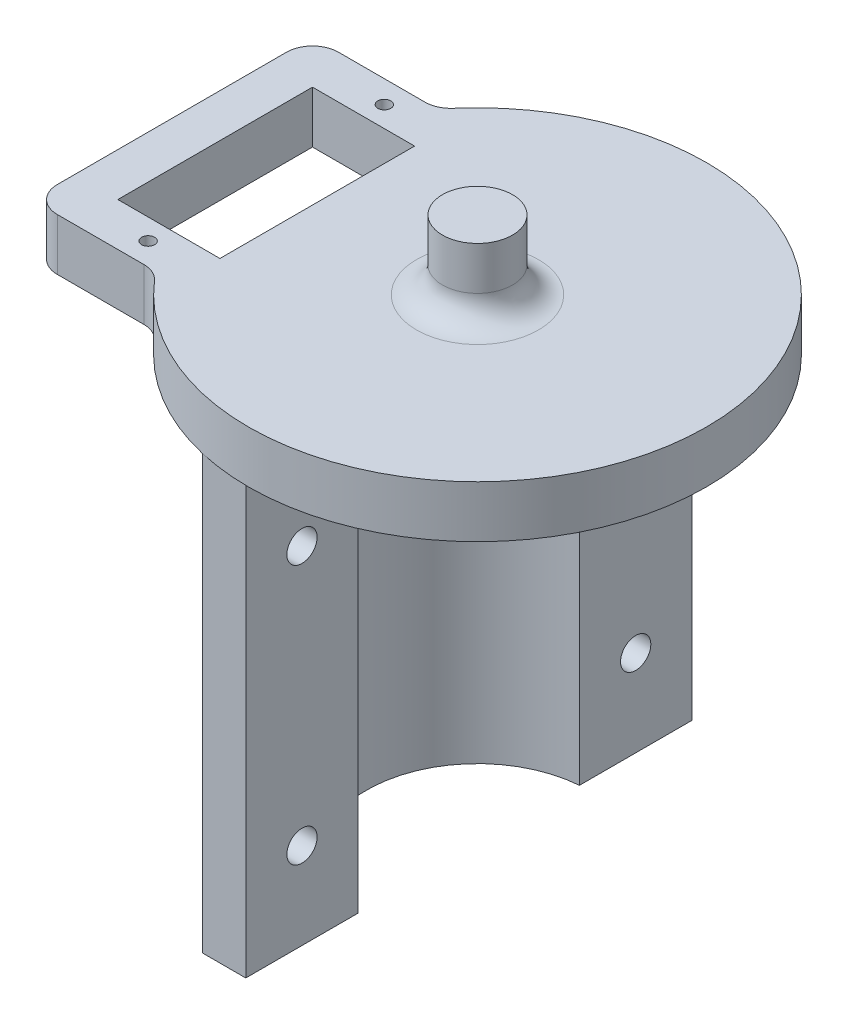
SolidWorks part; units mm, degrees
ref_plane "Front Plane" through (0, 0, 0) normal (0, 0, 1) x (1, 0, 0)
ref_plane "Top Plane" through (0, 0, 0) normal (0, 1, 0) x (1, 0, 0)
ref_plane "Right Plane" through (0, 0, 0) normal (1, 0, 0) x (0, 0, -1)
sketch "Sketch6" plane through (0, 0, 0) normal (0, -1, 0) x (1, 0, 0)
  line L5 (-1, 25.7848) -> (-1, 12.786)
  line L6 (-1, 25.7848) -> (-6, 25.7848)
  line L7 (-6, 25.7848) -> (-6, 16.7848)
  line L8 (-6, -16.7848) -> (-6, -25.7848)
  line L9 (-6, -25.7848) -> (-1, -25.7848)
  line L10 (-1, -25.7848) -> (-1, -12.786)
  line L11 (-12.825, 0) -> (-17.825, 0) construction
  arc A0 (-1, 12.786) -> (-1, -12.786) centre (0, 0) ccw
  arc A1 (-6, 16.7848) -> (-6, -16.7848) centre (0, 0) ccw
  dimension "D1" = 25.65
  dimension "D2" = 5
  dimension "D3" = 1
  dimension "D4" = 9
extrude "Boss-Extrude4" add sketch "Sketch6" along normal blind 50
sketch "Sketch7" plane through (-1, 0, 0) normal (1, 0, 0) x (0, 0, -1)
  line L0 (-19.2854, -50) -> (-19.2854, 0) construction
  line L3 (0, 0) -> (0, -50) construction
  line L6 (-25.7848, -25) -> (25.7848, -25) construction
  line L11 (-12.786, 0) -> (-25.7848, 0) construction
  line L12 (-12.786, -50) -> (-25.7848, -50) construction
  line L13 (-25.7848, -50) -> (-25.7848, 0) construction
  line L14 (25.7848, -50) -> (25.7848, 0) construction
  line L15 (-12.786, -50) -> (12.786, -50) construction
  circle A0 centre (-19.2854, -10) radius 1.75
  circle A1 centre (-19.2854, -40) radius 1.75
  circle A2 centre (19.2854, -40) radius 1.75
  circle A3 centre (19.2854, -10) radius 1.75
  dimension "D1" = 10
  dimension "D2" = 3.5
extrude "Cut-Extrude1" cut sketch "Sketch7" against normal through all
sketch "Sketch8" plane through (0, 0, 0) normal (0, 1, 0) x (1, 0, 0)
  line L0 (-24.4208, -13.65) -> (-24.4208, 13.65) construction
  line L1 (-30.3208, -11.25) -> (-18.5208, -11.25)
  line L2 (-30.3208, -11.25) -> (-30.3208, 11.25)
  line L3 (-30.3208, 11.25) -> (-18.5208, 11.25)
  line L4 (-18.5208, -11.25) -> (-18.5208, 11.25)
  line L5 (-32.3208, -16.25) -> (-22.319, -16.25)
  line L6 (-35.3208, -13.25) -> (-35.3208, 13.25)
  line L7 (-32.3208, 16.25) -> (-22.319, 16.25)
  circle A1 centre (-24.4208, 13.65) radius 0.75
  circle A2 centre (-24.4208, -13.65) radius 0.75
  arc A3 (-20.0472, -17.2906) -> (-20.0472, 17.2906) centre (0, 0) ccw
  arc A4 (-32.3208, -16.25) -> (-35.3208, -13.25) centre (-32.3208, -13.25) cw
  arc A5 (-35.3208, 13.25) -> (-32.3208, 16.25) centre (-32.3208, 13.25) cw
  arc A6 (-22.319, 16.25) -> (-20.0472, 17.2906) centre (-22.319, 19.25) ccw
  arc A7 (-22.319, -16.25) -> (-20.0472, -17.2906) centre (-22.319, -19.25) cw
  circle A8 centre (-24.4208, 5.35) radius 5.9 construction
  point P7 (-18.5208, 0)
  point P13 (-24.4208, -11.25)
  point P18 (-24.4208, 0)
  point P24 (-35.3208, 0)
  dimension "D1" = 5
  dimension "D4" = 1.5
  dimension "D7" = 5
  dimension "D8" = 3
  dimension "D9" = 3
  dimension "D10" = 11.8
  dimension "D2" = 11.8
  dimension "D3" = 22.5
  dimension "D5" = 27.3
  dimension "D6" = 25
extrude "Boss-Extrude5" add sketch "Sketch8" along normal blind 6
sketch "Sketch9" plane through (0, 6, 0) normal (0, 1, 0) x (1, 0, 0)
  circle A0 centre (0, 0) radius 4.05
  dimension "D1" = 8.1
extrude "Boss-Extrude6" add sketch "Sketch9" along normal blind 8
fillet "Fillet1" radius 3 1 edges at (0, 6, 4.05)
